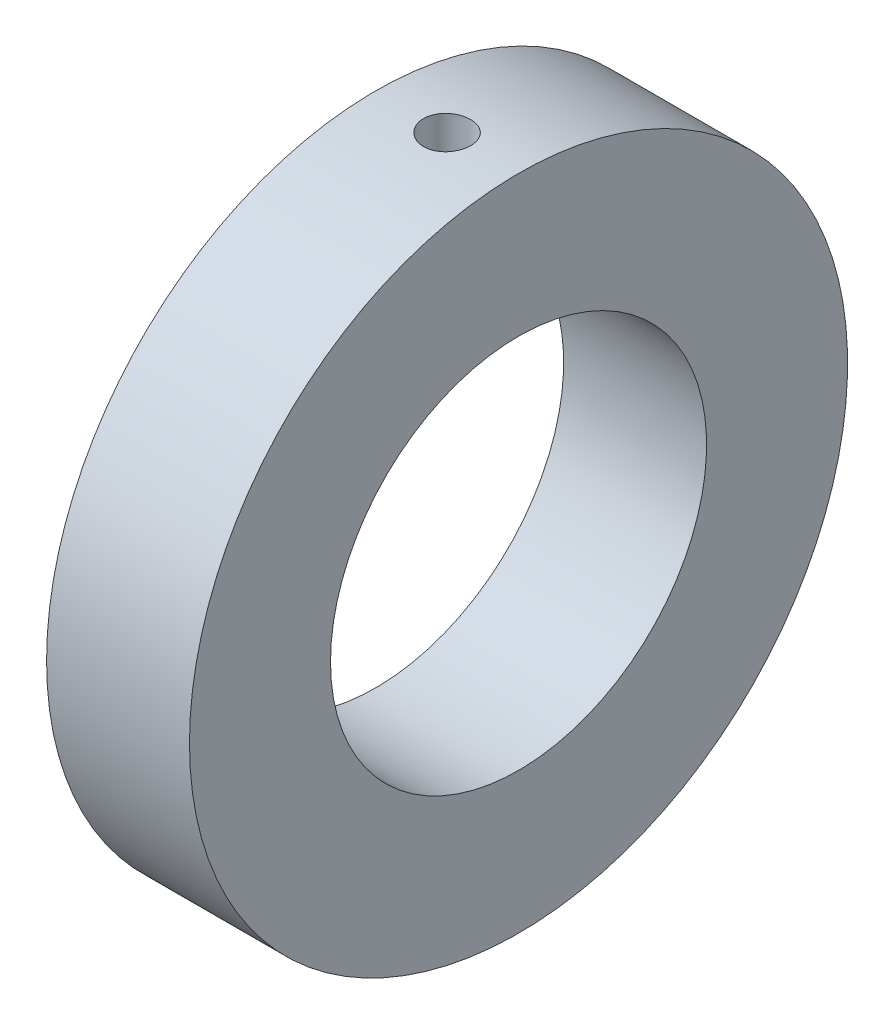
SolidWorks part; units mm, degrees
material "AISI 1020 Steel, Cold Rolled"
ref_plane "Front" through (0, 0, 0) normal (0, 0, 1) x (1, 0, 0)
ref_plane "Top" through (0, 0, 0) normal (0, 1, 0) x (1, 0, 0)
ref_plane "Right" through (0, 0, 0) normal (1, 0, 0) x (0, 0, -1)
sketch "Sketch1" plane through (0, 0, 0) normal (0, 1, 0) x (1, 0, 0)
  line L0 (-13.5112, 8.7312) -> (10.6302, 8.7312) construction
  line L1 (2.413, 2.3813) -> (-2.413, 2.3812)
  line L2 (2.413, 2.3813) -> (2.413, -2.3812)
  line L3 (2.413, -2.3812) -> (-2.413, -2.3813)
  line L4 (-2.413, 2.3812) -> (-2.413, -2.3813)
  line L5 (2.413, 2.3813) -> (-2.413, -2.3813) construction
  line L6 (2.413, -2.3812) -> (-2.413, 2.3812) construction
  point P0 (0, 0)
  point P8 (0, -2.3812)
  dimension "D1" = 12.7
  dimension "D2" = 22.225
  dimension "D3" = 4.826
revolve "Revolve1" add sketch "Sketch1" angle 360 about L0
ref_plane "Plane1" through (0, 11.1125, 0) normal (0, 1, 0) x (1, 0, 0)
ref_plane "Plane2" through (0, 11.1125, 0) normal (0, 1, 0) x (1, 0, 0)
ref_plane "Plane3" through (0, 11.1125, 0) normal (0, 1, 0) x (1, 0, 0)
ref_plane "Plane4" through (0, 11.1125, 0) normal (0, 1, 0) x (1, 0, 0)
hole_wizard "1/16 (0.0625) Diameter Hole1" positions "Sketch12" profile "Sketch13" hole size "1/16" standard "ANSI Inch"
sketch "Sketch12" plane through (0, 11.1125, 0) normal (0, 1, 0) x (1, 0, 0)
  line L0 (-2.413, 8.7312) -> (2.413, 8.7312) construction
  line L1 (-2.413, 19.8438) -> (-2.413, -2.3812) construction
  line L2 (2.413, -2.3812) -> (2.413, 19.8437) construction
  point P0 (0, 8.7312)
sketch "Sketch13" plane through (0, 11.1125, -8.7312) normal (1, 0, 0) x (0, 0, 1)
  line L0 (0, 0) -> (0, 13.1769)
  line L1 (0, 13.1769) -> (0.7937, 12.7)
  line L2 (0.7937, 12.7) -> (0.7937, 0)
  line L5 (0.7937, 0) -> (0, 0)
  line L10 (0, 13.1769) -> (-0.7938, 12.7) construction
  line L11 (0, -6.35) -> (0, 107.95) construction
  dimension "Hole Dia." = 1.5875
  dimension "Hole Depth" = 12.7
  dimension "Drill Angle" = 118
